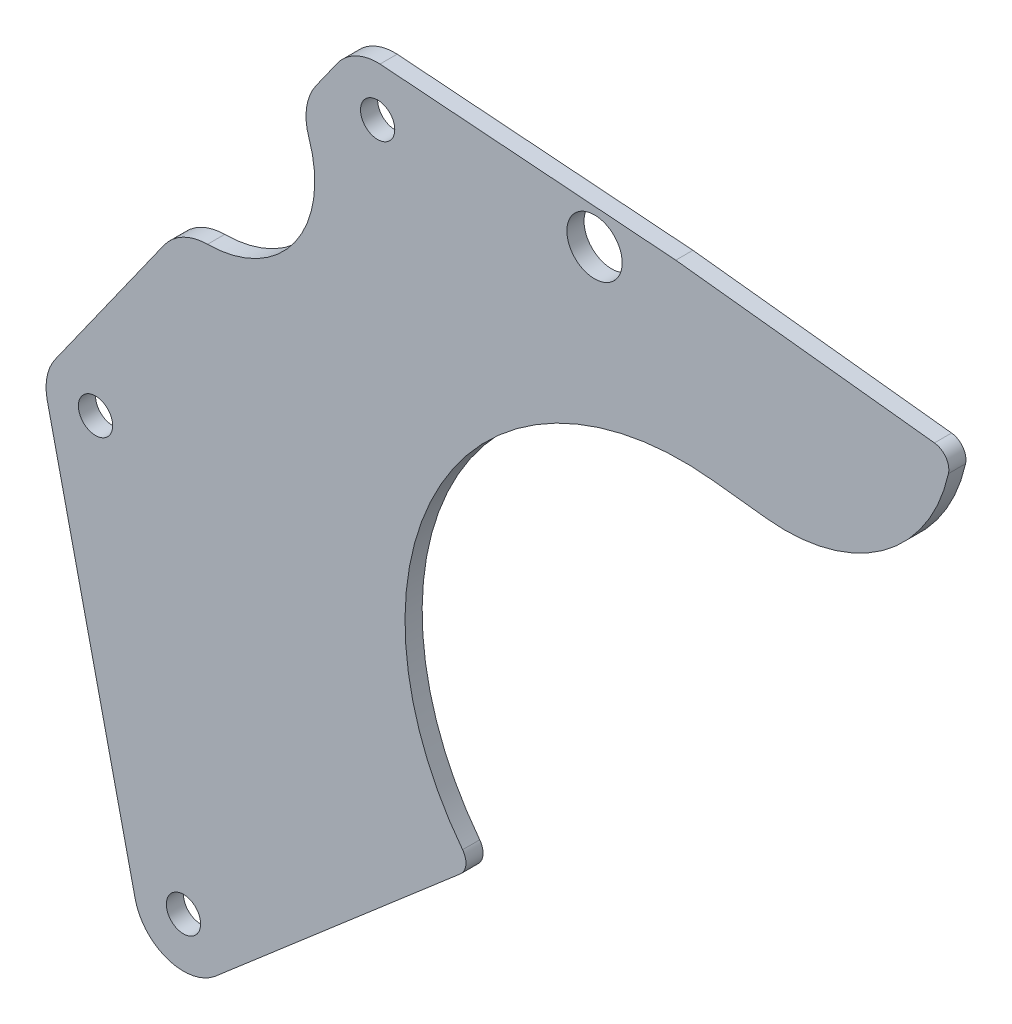
SolidWorks part; units mm, degrees
ref_plane "Front Plane" through (0, 0, 0) normal (0, 0, 1) x (1, 0, 0)
ref_plane "Top Plane" through (0, 0, 0) normal (0, 1, 0) x (1, 0, 0)
ref_plane "Right Plane" through (0, 0, 0) normal (1, 0, 0) x (0, 0, -1)
sketch "Sketch1" plane through (0, 0, 0) normal (0, 0, 1) x (1, 0, 0)
  line L0 (-1.2261, 83.0414) -> (9.1592, 81.8805)
  line L1 (14.6634, -16.9991) -> (-54.5657, -76.6416) construction
  line L2 (-56.0397, 87.1189) -> (-1.2261, 83.0414) construction
  line L3 (-56.0397, 87.1189) -> (-1.2261, 83.0414)
  line L4 (14.6634, -16.9991) -> (-54.5657, -76.6416)
  line L5 (0.0073, 0.0127) -> (-86.9522, -74.9051)
  line L6 (9.1592, 81.8805) -> (5.7199, 51.1142)
  line L7 (-86.9522, -74.9051) -> (-87.4115, -75.209)
  line L9 (-63.9675, 83.2657) -> (-118.6287, 6.262)
  line L10 (-101.4233, -69.5879) -> (-118.6287, 6.262)
  line L11 (-99.932, -83.4966) -> (-101.4457, -84.4985)
  circle A1 centre (0.0073, 0.0127) radius 82.3777
  circle A2 centre (-92.4757, -67.5582) radius 3.175
  circle A3 centre (-108.7742, 4.2939) radius 3.175
  circle A4 centre (-56.4858, 77.9548) radius 3.175
  circle A5 centre (-56.4858, 77.9548) radius 9.175
  circle A6 centre (-108.7742, 4.2939) radius 9.175
  circle A7 centre (-92.4757, -67.5582) radius 9.175
  circle A8 centre (-16.2857, 77.6468) radius 3.175 construction
  circle A9 centre (-16.2857, 77.6468) radius 3.175
  circle A10 centre (-16.2857, 77.6468) radius 5.125
  circle A11 centre (0.0073, 0.0127) radius 51.4198
  dimension "D1" = 6.35
  dimension "D2" = 6.35
  dimension "D3" = 6.35
  dimension "D5" = 10.25
  dimension "D4" = 6
extrude "Boss-Extrude1" add sketch "Sketch1" against normal blind 3.175 contours A10 A1 L0 L3 A5 L9 A6 L10 A7 L7 | A7 A2 | A6 A3 | L3 A5 A4 | A10 A1 L7 A11 L6
sketch "Sketch2" plane through (0, 0, 0) normal (0, 0, 1) x (1, 0, 0)
  line L0 (9.1592, 81.8805) -> (19.0973, 80.7695)
  line L1 (5.7199, 51.1142) -> (15.658, 50.0033)
  line L2 (19.0973, 80.7695) -> (49.8635, 77.3302)
  arc A0 (-11.669, 84.2088) -> (49.8635, 77.3302) centre (19.0973, 80.7695) ccw
  line M3 (5.7199, 51.1142) -> (9.1592, 81.8805)
  dimension "D1" = 10
extrude "Boss-Extrude2" add sketch "Sketch2" against normal up to surface (3.175 mm away) contours L0 A0 L2 | A0 L0 L1 M3 up to face at (-11.1607, 77.6468, -3.175)
fillet "Fillet1" radius 3 1 edges at (49.8635, 77.3302, -1.5875)
fillet "Fillet2" radius 3 1 edges at (-38.9491, -33.5492, -1.5875)
sketch "Sketch3" plane through (0, 0, -3.175) normal (0, 0, -1) x (-1, 0, 0)
  circle A0 centre (88.1391, 62.1932) radius 20
extrude "Cut-Extrude1" cut sketch "Sketch3" against normal blind 10
fillet "Fillet3" radius 10 2 edges at (-71.2838, 72.9589, -1.5875) (-92.7418, 42.73, -1.5875)
